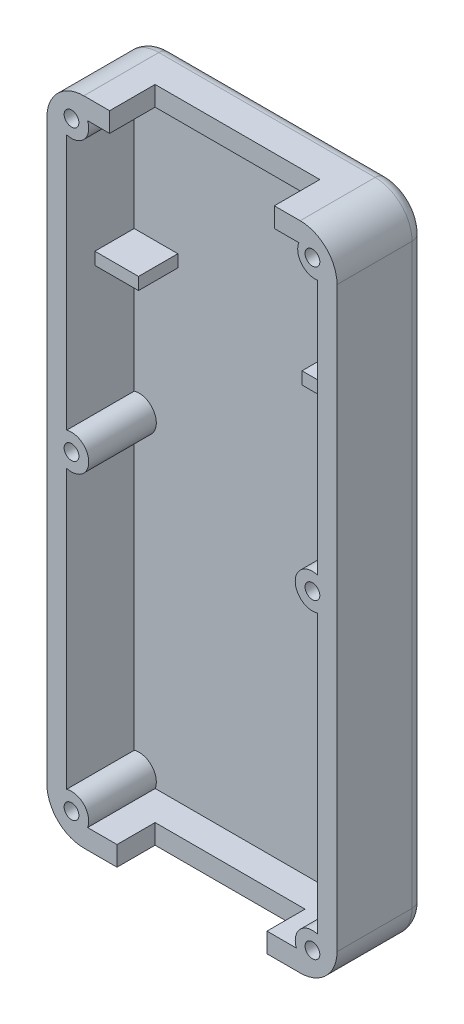
SolidWorks part; units mm, degrees
ref_plane "Front Plane" through (0, 0, 0) normal (0, 0, 1) x (1, 0, 0)
ref_plane "Top Plane" through (0, 0, 0) normal (0, 1, 0) x (1, 0, 0)
ref_plane "Right Plane" through (0, 0, 0) normal (1, 0, 0) x (0, 0, -1)
sketch "Sketch1" plane through (0, 0, 0) normal (0, 0, 1) x (1, 0, 0)
  line L1 (-40.6184, -1.5264) -> (-17.0184, -1.5264)
  line L2 (-40.6184, -1.5264) -> (-40.6184, -54.5264)
  line L3 (-40.6184, -54.5264) -> (-17.0184, -54.5264)
  line L4 (-17.0184, -1.5264) -> (-17.0184, -54.5264)
extrude "Boss-Extrude2" add sketch "Sketch1" along normal blind 7.1
shell "Shell1" thickness 1.6
fillet "Fillet2" radius 3 4 edges at (-17.0184, -1.5264, 3.55) (-17.0184, -54.5264, 3.55) (-40.6184, -54.5264, 3.55) (-40.6184, -1.5264, 3.55)
sketch "Sketch7" plane through (0, 0, 7.1) normal (0, 0, 1) x (1, 0, 0)
  line L6 (-40.6184, -4.5264) -> (-40.6184, -51.5264) construction
  line L7 (-17.0184, -51.5264) -> (-17.0184, -4.5264) construction
  line L8 (-39.0184, -52.9264) -> (-18.6184, -52.9264) construction
  line L9 (-34.9184, -52.9264) -> (-22.7184, -52.9264)
  line L10 (-34.9184, -52.9264) -> (-34.9184, -54.5264)
  line L11 (-34.9184, -54.5264) -> (-22.7184, -54.5264)
  line L12 (-22.7184, -52.9264) -> (-22.7184, -54.5264)
  line L13 (-37.6184, -54.5264) -> (-20.0184, -54.5264) construction
  dimension "D3" = 5.7
  dimension "D4" = 5.7
extrude "Cut-Extrude1" cut sketch "Sketch7" against normal blind 3.1 contours L9 L12 L11 L10
sketch "Sketch8" plane through (0, 0, 7.1) normal (0, 0, 1) x (1, 0, 0)
  line L0 (-20.0184, -1.5264) -> (-37.6184, -1.5264) construction
  line L1 (-35.5184, -1.5264) -> (-22.1184, -1.5264)
  line L2 (-35.5184, -1.5264) -> (-35.5184, -3.1264)
  line L3 (-35.5184, -3.1264) -> (-22.1184, -3.1264)
  line L4 (-22.1184, -1.5264) -> (-22.1184, -3.1264)
  line L5 (-18.6184, -3.1264) -> (-39.0184, -3.1264) construction
  line L6 (-40.6184, -4.5264) -> (-40.6184, -51.5264) construction
  line L7 (-17.0184, -51.5264) -> (-17.0184, -4.5264) construction
  dimension "D1" = 5.1
  dimension "D2" = 5.1
extrude "Cut-Extrude2" cut sketch "Sketch8" against normal blind 3.7
sketch "Sketch9" plane through (0, 0, 1.6) normal (0, 0, 1) x (1, 0, 0)
  line L5 (-18.6184, -52.9264) -> (-18.6184, -3.1264) construction
  line L6 (-18.6184, -14.3264) -> (-22.1684, -14.3264)
  line L7 (-18.6184, -14.3264) -> (-18.6184, -15.3264)
  line L8 (-18.6184, -15.3264) -> (-22.1684, -15.3264)
  line L9 (-22.1684, -14.3264) -> (-22.1684, -15.3264)
  line L10 (-20.0184, -1.5264) -> (-22.1184, -1.5264) construction
  line L11 (-39.0184, -3.1264) -> (-39.0184, -52.9264) construction
  line L12 (-39.0184, -14.3264) -> (-35.4684, -14.3264)
  line L13 (-39.0184, -14.3264) -> (-39.0184, -15.3264)
  line L14 (-39.0184, -15.3264) -> (-35.4684, -15.3264)
  line L15 (-35.4684, -14.3264) -> (-35.4684, -15.3264)
  line L16 (-35.5184, -1.5264) -> (-37.6184, -1.5264) construction
  dimension "D1" = 12.8
  dimension "D2" = 12.8
extrude "Boss-Extrude3" add sketch "Sketch9" along normal blind 3.2
sketch "Sketch10" plane through (0, 0, 7.1) normal (0, 0, 1) x (1, 0, 0)
  circle A6 centre (-38.6184, -52.4264) radius 1.4
  circle A7 centre (-19.0184, -52.4264) radius 1.4
  circle A8 centre (-38.6184, -27.1264) radius 1.4
  circle A9 centre (-19.0184, -27.1264) radius 1.4
  circle A10 centre (-18.8184, -3.6264) radius 1.4
  circle A11 centre (-38.6184, -3.6264) radius 1.4
extrude "Boss-Extrude4" add sketch "Sketch10" against normal blind 7.1
sketch "Sketch11" plane through (0, 0, 7.1) normal (0, 0, 1) x (1, 0, 0)
  circle A0 centre (-38.6184, -3.6264) radius 0.6
  circle A1 centre (-19.0184, -3.6264) radius 0.6
  circle A2 centre (-38.6184, -52.4264) radius 0.6
  circle A3 centre (-19.0184, -52.4264) radius 0.6
  circle A4 centre (-38.6184, -27.1264) radius 0.6
  circle A5 centre (-19.0184, -27.1264) radius 0.6
  dimension "D1" = 2
  dimension "D2" = 2
  dimension "D3" = 2
extrude "Cut-Extrude4" cut sketch "Sketch11" against normal blind 7.1
fillet "Fillet3" radius 1 8 edges at (-39.7397, -2.4051, 0) (-28.8184, -1.5264, 0) (-17.897, -2.4051, 0) (-17.0184, -28.0264, 0) (-17.897, -53.6477, 0) (-28.8184, -54.5264, 0) (-39.7397, -53.6477, 0) (-40.6184, -28.0264, 0)
sketch "Sketch12" plane through (0, 0, 1.6) normal (0, 0, 1) x (1, 0, 0)
  line L0 (-37.3107, -3.1264) -> (-20.126, -3.1264)
  line L5 (-39.0184, -4.968) -> (-39.0184, -25.7847)
  line L6 (-39.0184, -28.468) -> (-39.0184, -51.0847)
  line L7 (-37.3107, -52.9264) -> (-20.326, -52.9264)
  line L8 (-18.6184, -51.0847) -> (-18.6184, -28.468)
  line L9 (-18.6184, -25.7847) -> (-18.6184, -4.774)
  line L15 (-35.5281, -3.1264) -> (-22.1097, -3.1264)
  line L16 (-35.5281, -3.1264) -> (-35.5281, -4.774)
  line L17 (-35.5281, -4.774) -> (-22.1097, -4.774)
  line L18 (-22.1097, -3.1264) -> (-22.1097, -4.774)
  line L19 (-34.9184, -52.9264) -> (-22.7255, -52.9264)
  line L20 (-34.9184, -52.9264) -> (-34.9184, -51.4313)
  line L21 (-34.9184, -51.4313) -> (-22.7255, -51.4313)
  line L22 (-22.7255, -52.9264) -> (-22.7255, -51.4313)
  line L23 (-39.0184, -14.3264) -> (-35.4684, -14.3264)
  line L24 (-39.0184, -14.3264) -> (-39.0184, -15.3264)
  line L25 (-39.0184, -15.3264) -> (-35.4684, -15.3264)
  line L26 (-35.4684, -14.3264) -> (-35.4684, -15.3264)
  line L27 (-18.6184, -14.3264) -> (-22.1684, -14.3264)
  line L28 (-18.6184, -14.3264) -> (-18.6184, -15.3264)
  line L29 (-18.6184, -15.3264) -> (-22.1684, -15.3264)
  line L30 (-22.1684, -14.3264) -> (-22.1684, -15.3264)
  arc A0 (-39.0184, -4.968) -> (-37.3107, -3.1264) centre (-38.6184, -3.6264) ccw
  arc A1 (-20.126, -3.1264) -> (-18.6184, -4.774) centre (-19.0184, -3.6264) ccw
  arc A2 (-18.6184, -25.7847) -> (-18.6184, -28.468) centre (-19.0184, -27.1264) ccw
  arc A3 (-18.6184, -25.7847) -> (-18.6184, -28.468) centre (-19.0184, -27.1264) ccw construction
  arc A4 (-39.0184, -25.7847) -> (-39.0184, -28.468) centre (-38.6184, -27.1264) cw
  arc A5 (-39.0184, -28.468) -> (-39.0184, -25.7847) centre (-38.6184, -27.1264) ccw construction
  arc A6 (-39.0184, -51.0847) -> (-37.3107, -52.9264) centre (-38.6184, -52.4264) cw
  arc A7 (-37.3107, -52.9264) -> (-39.0184, -51.0847) centre (-38.6184, -52.4264) ccw construction
  arc A8 (-20.326, -52.9264) -> (-18.6184, -51.0847) centre (-19.0184, -52.4264) cw
